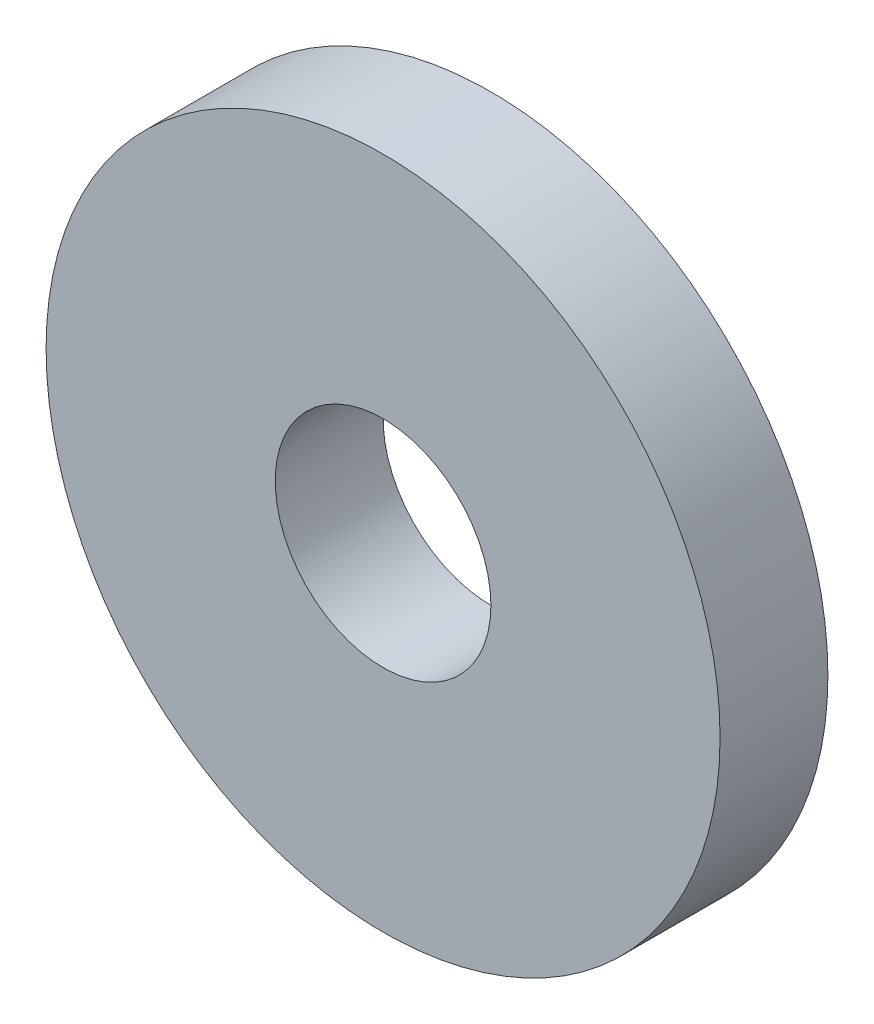
SolidWorks part; units mm, degrees
ref_plane "Спереди" through (0, 0, 0) normal (0, 0, 1) x (1, 0, 0)
ref_plane "Сверху" through (0, 0, 0) normal (0, 1, 0) x (1, 0, 0)
ref_plane "Справа" through (0, 0, 0) normal (1, 0, 0) x (0, 0, -1)
sketch "Эскиз1" plane through (0, 0, 0) normal (0, 0, 1) x (1, 0, 0)
  circle A0 centre (0, 0) radius 12.5
  circle A2 centre (0, 0) radius 4
  dimension "D1" = 25
  dimension "D2" = 8
extrude "Бобышка-Вытянуть1" add sketch "Эскиз1" along normal blind 4
